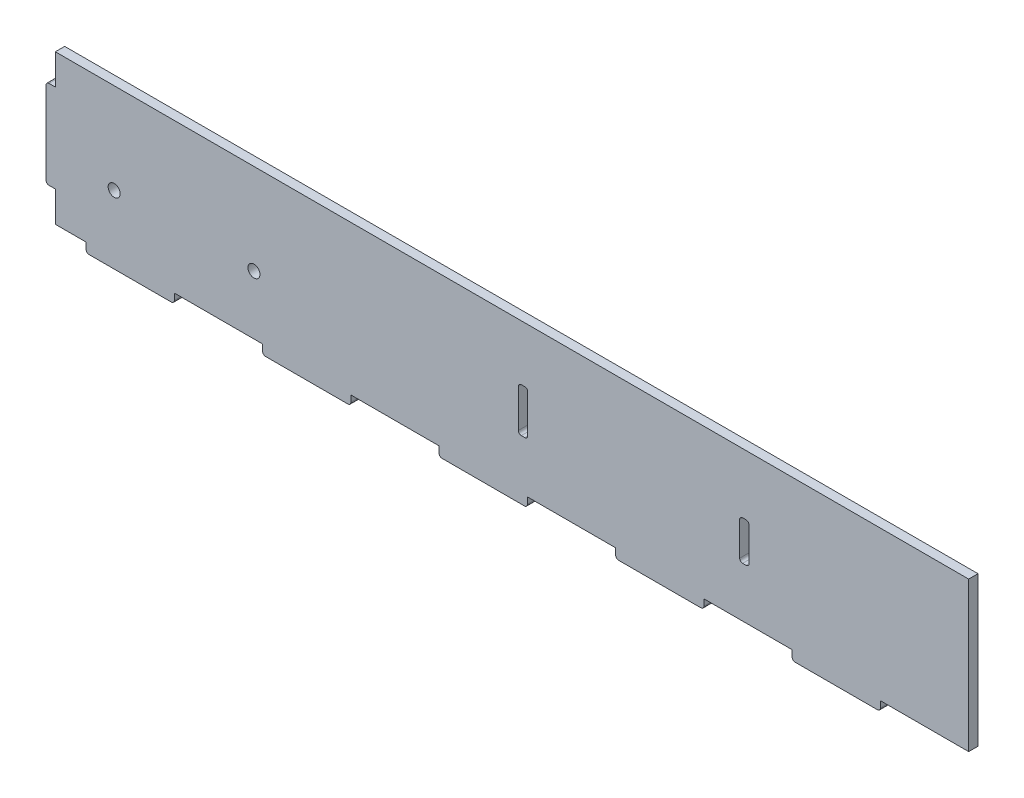
SolidWorks part; units mm, degrees
ref_plane "Front Plane" through (0, 0, 0) normal (0, 0, 1) x (1, 0, 0)
ref_plane "Top Plane" through (0, 0, 0) normal (0, 1, 0) x (1, 0, 0)
ref_plane "Right Plane" through (0, 0, 0) normal (1, 0, 0) x (0, 0, -1)
sketch "Sketch1" plane through (0, 0, 0) normal (0, 0, 1) x (1, 0, 0)
  line L1 (-155.225, -25.4) -> (155.225, -25.4)
  line L2 (-155.225, -25.4) -> (-155.225, 25.4)
  line L3 (-155.225, 25.4) -> (155.225, 25.4)
  line L4 (155.225, -25.4) -> (155.225, 25.4)
  line L5 (-155.225, -25.4) -> (155.225, 25.4) construction
  line L6 (-155.225, 25.4) -> (155.225, -25.4) construction
  point P0 (0, 0)
  dimension "D1" = 310.45
  dimension "D2" = 50.8
extrude "Boss-Extrude1" add sketch "Sketch1" along normal blind 3.175
sketch "Sketch2" plane through (0, 0, 3.175) normal (0, 0, 1) x (1, 0, 0)
  line L0 (80.555, 25.4) -> (80.555, -28.265) construction
  line L1 (155.225, 25.4) -> (-155.225, 25.4) construction
  line L2 (155.225, -25.4) -> (155.225, 25.4) construction
  line L3 (-155.225, -25.4) -> (155.225, -25.4) construction
  line L4 (80.555, 5.0225) -> (77.38, 5.0225)
  line L5 (80.555, 5.0225) -> (80.555, -8.4)
  line L6 (80.555, -8.4) -> (77.38, -8.4)
  line L7 (77.38, 5.0225) -> (77.38, -8.4)
  line L8 (5.33, 25.4) -> (5.33, -25.8862) construction
  line L9 (-135.225, 25.4) -> (-135.225, -25.4) construction
  line L10 (5.33, 6.6) -> (2.155, 6.6)
  line L11 (5.33, 6.6) -> (5.33, -8.4)
  line L12 (5.33, -8.4) -> (2.155, -8.4)
  line L13 (2.155, 6.6) -> (2.155, -8.4)
  line L14 (-155.225, -5.4) -> (-82.8714, -5.4) construction
  line L15 (-155.225, 25.4) -> (-155.225, -25.4) construction
  circle A0 centre (-135.225, -5.4) radius 2.05
  circle A1 centre (-87.725, -5.4) radius 2.0505
  point P6 (155.225, 0)
  dimension "D10" = 4.1
  dimension "D11" = 4.101
  dimension "D1" = 74.67
  dimension "D2" = 17
  dimension "D3" = 3.175
  dimension "D4" = 72.05
  dimension "D5" = 3.175
  dimension "D6" = 15
  dimension "D7" = 17
  dimension "D8" = 20
  dimension "D9" = 20
  dimension "D12" = 47.5
extrude "Cut-Extrude1" cut sketch "Sketch2" against normal through all
sketch "Sketch3" plane through (-155.225, 0, 0) normal (-1, 0, 0) x (0, 0, 1)
  line L0 (0, 0) -> (3.175, 0) construction
  line L1 (3.175, 25.4) -> (3.175, -25.4) construction
  line L3 (0, -15) -> (3.175, -15)
  line L4 (0, -15) -> (0, 15)
  line L5 (0, 15) -> (3.175, 15)
  line L6 (3.175, -15) -> (3.175, 15)
  line L7 (0, -15) -> (3.175, 15) construction
  line L8 (0, 15) -> (3.175, -15) construction
  point P5 (1.5875, 0)
  dimension "D1" = 30
extrude "Boss-Extrude2" add sketch "Sketch3" along normal blind 3.175
sketch "Sketch4" plane through (0, -25.4, 0) normal (0, -1, 0) x (1, 0, 0)
  line L0 (-155.225, 3.175) -> (155.225, 3.175) construction
  line L1 (125.225, 3.175) -> (95.225, 3.175)
  line L2 (125.225, 3.175) -> (125.225, 0)
  line L3 (125.225, 0) -> (95.225, 0)
  line L4 (95.225, 3.175) -> (95.225, 0)
  line L5 (-155.225, 0) -> (155.225, 0) construction
  line L7 (155.225, 3.175) -> (155.225, 0) construction
  line L8 (65.225, 3.175) -> (65.225, 0)
  line L9 (65.225, 3.175) -> (35.225, 3.175)
  line L10 (35.225, 3.175) -> (35.225, 0)
  line L11 (65.225, 0) -> (35.225, 0)
  line L12 (5.225, 3.175) -> (5.225, 0)
  line L13 (5.225, 3.175) -> (-24.775, 3.175)
  line L14 (-24.775, 3.175) -> (-24.775, 0)
  line L15 (5.225, 0) -> (-24.775, 0)
  line L16 (-54.775, 3.175) -> (-54.775, 0)
  line L17 (-54.775, 3.175) -> (-84.775, 3.175)
  line L18 (-84.775, 3.175) -> (-84.775, 0)
  line L19 (-54.775, 0) -> (-84.775, 0)
  line L20 (-114.775, 3.175) -> (-114.775, 0)
  line L21 (-114.775, 3.175) -> (-144.775, 3.175)
  line L22 (-144.775, 3.175) -> (-144.775, 0)
  line L23 (-114.775, 0) -> (-144.775, 0)
  line L24 (125.225, 3.175) -> (65.225, 3.175) construction
  dimension "D1" = 30
  dimension "D2" = 30
  dimension "D4" = 60
  dimension "D3" = 5
extrude "Boss-Extrude3" add sketch "Sketch4" along normal blind 3.175
fillet "Fillet1" radius 1 20 edges at (2.155, -8.4, 1.5875) (5.33, -8.4, 1.5875) (5.33, 6.6, 1.5875) (2.155, 6.6, 1.5875) (77.38, 5.0225, 1.5875) (80.555, 5.0225, 1.5875) (77.38, -8.4, 1.5875) (80.555, -8.4, 1.5875) (125.225, -28.575, 1.5875) (95.225, -28.575, 1.5875) (65.225, -28.575, 1.5875) (35.225, -28.575, 1.5875) (5.225, -28.575, 1.5875) (-24.775, -28.575, 1.5875) (-54.775, -28.575, 1.5875) (-84.775, -28.575, 1.5875) (-114.775, -28.575, 1.5875) (-144.775, -28.575, 1.5875) (-158.4, -15, 1.5875) (-158.4, 15, 1.5875)
